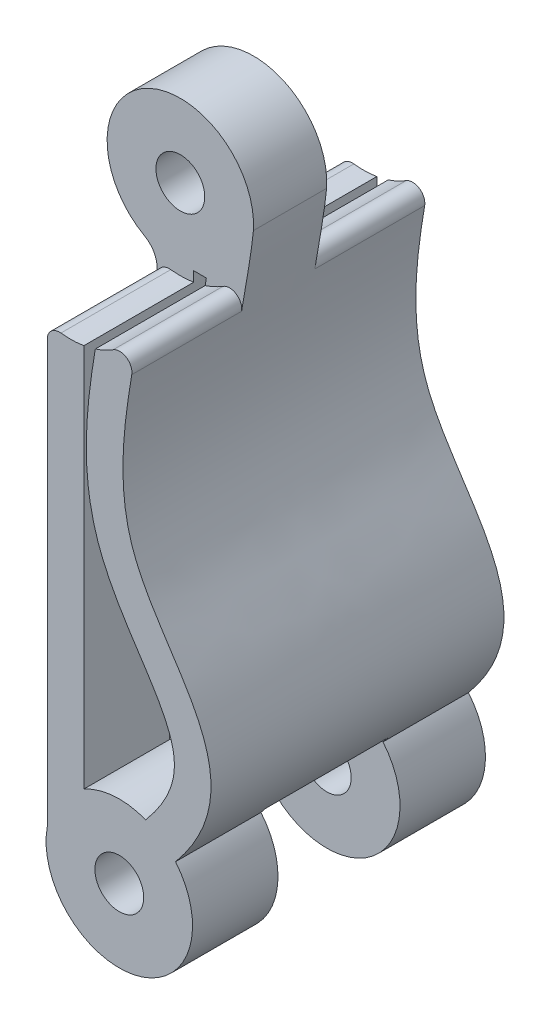
SolidWorks part; units mm, degrees
ref_plane "Front Plane" through (0, 0, 0) normal (0, 0, 1) x (1, 0, 0)
ref_plane "Top Plane" through (0, 0, 0) normal (0, 1, 0) x (1, 0, 0)
ref_plane "Right Plane" through (0, 0, 0) normal (1, 0, 0) x (0, 0, -1)
sketch "Sketch1" plane through (0, 0, 0) normal (0, 0, 1) x (1, 0, 0)
  line L3 (0.9027, 23.1193) -> (0.9027, 44.7293) construction
  line L4 (0.9027, 44.7293) -> (-1.0973, 44.7293) construction
  line L5 (-2.0488, 41.8842) -> (-2.0488, 23.6567)
  line L6 (-0.0313, 41.8842) -> (-0.5488, 41.8842)
  line L7 (-0.5488, 41.8842) -> (-0.5488, 25.7448)
  line L10 (-0.5488, 43.3332) -> (-0.5488, 23.4977) construction
  line L12 (1003.2054, 25.0421) -> (3.2054, 25.0421) construction
  line L13 (-2.0488, 41.8842) -> (49997.9512, 41.8842) construction
  line L14 (-0.5488, 25.0421) -> (-49996.7946, 25.0421) construction
  arc A0 (-2.0488, 41.8842) -> (1.896, 44.5297) centre (-1.0973, 44.7293) cw
  arc A2 (-2.0488, 23.6567) -> (3.2054, 25.0421) centre (0.9027, 23.1193) ccw
  circle A3 centre (-1.0973, 44.7293) radius 1
  circle A4 centre (0.9027, 23.1193) radius 1
  arc A7 (-0.5488, 23.4977) -> (0.9027, 24.6193) centre (0.9027, 23.1193) ccw construction
  arc A8 (-0.5488, 43.3332) -> (0.4006, 44.6513) centre (-1.0973, 44.7293) cw construction
  arc A9 (1.9829, 25.918) -> (-0.5488, 25.7448) centre (0.9027, 23.1193) ccw
  spline S0 degree 3 poles (1.896, 44.5297) (1.6161, 41.7589) (-0.9369, 33.9552) (6.8447, 29.4175) (3.2054, 25.0421) knots 0 0 0 0 0.461185 1 1 1 1
  spline S1 degree 1 poles (0.4006, 44.6513) (0.9027, 24.6193) knots 0 0 1 1 construction
  spline S2 degree 3 poles (0.4006, 44.6513) (0.3814, 44.4652) (0.3367, 44.1044) (0.2163, 43.3069) (0.0657, 42.4502) (-0.0914, 41.5355) (-0.2432, 40.5851) (-0.402, 39.3533) (-0.4791, 37.8282) (-0.3759, 36.2754) (0.01, 34.6811) (0.9413, 32.7707) (2.0354, 31.2469) (2.8047, 29.9095) (3.1286, 29.0309) (3.1964, 28.2674) (3.0323, 27.5503) (2.6663, 26.8291) (2.3349, 26.3502) (2.1068, 26.0672) (2.0129, 25.9541) (1.9549, 25.8844) (1.8019, 25.7008) (1.4593, 25.2881) (1.1253, 24.887) (0.9027, 24.6193) knots 0.001801 0.001801 0.001801 0.001801 0.034767 0.067734 0.132717 0.165683 0.1996 0.265533 0.331467 0.3974 0.463333 0.529266 0.661132 0.727066 0.792999 0.858932 0.924865 0.957832 0.990798 0.99904 1.001358 1.005479 1.00754 1.023765 1.056732 1.056732 1.056732 1.056732 only from (-0.0313, 41.8842) to (1.9829, 25.918)
  dimension "D1" = 2
  dimension "D2" = 3
  dimension "D3" = 21.61
  dimension "D4" = 2
  dimension "D5" = 1.5
  dimension "D6" = 6
  dimension "D7" = 1.5
extrude "Boss-Extrude1" add sketch "Sketch1" along normal blind 12
ref_plane "midplane" through (0, 0, 6) normal (0, 0, 1) x (1, 0, 0)
sketch "Sketch2" plane through (0, 0, 12) normal (0, 0, 1) x (1, 0, 0)
  circle A4 centre (-1.0973, 44.7293) radius 3.3
  dimension "D1" = 6.6
extrude "Cut-Extrude1" cut sketch "Sketch2" against normal blind 4.5
mirror "Mirror1" about plane through (0, 0, 6) normal (0, 0, 1) of "Cut-Extrude1"
sketch "Sketch3" plane through (0, 0, 6) normal (0, 0, 1) x (1, 0, 0)
  circle A2 centre (0.9027, 23.1193) radius 3.3
  dimension "D1" = 6.6
extrude "Cut-Extrude2" cut sketch "Sketch3" against normal blind 2.5 and the other way blind 2.5
fillet "Fillet1" radius 0.5 4 edges at (-2.0488, 41.5694, 2.25) (-2.0488, 41.5694, 9.75) (1.6708, 42.9328, 2.25) (1.6708, 42.9328, 9.75)
fillet "Fillet2" radius 1 1 edges at (-2.0488, 41.8842, 6)
equation "\"axle-diameter\"=2"
equation "\"switch-thickness\"=12"
equation "\"base-width\"=4.0"
equation "\"axle-bushing-radius\"=3"
equation "\"D1@Sketch1\"=\"axle-diameter\""
equation "\"D2@Sketch1\"=\"axle-bushing-radius\""
equation "\"D1@Cut-Extrude1\"=\"switch-thickness\"/3+\"clearance\""
equation "\"D1@Cut-Extrude2\"=\"switch-thickness\"/6+\"clearance\""
equation "\"D2@Cut-Extrude2\"=\"switch-thickness\"/6+\"clearance\""
equation "\"D1@Boss-Extrude1\"=\"switch-thickness\""
equation "\"D1@Sketch2\"=\"axle-bushing-radius\"*2.2"
equation "\"D1@Sketch3\"=\"axle-bushing-radius\"*2.2"
equation "\"clearance\"= 0.5"
